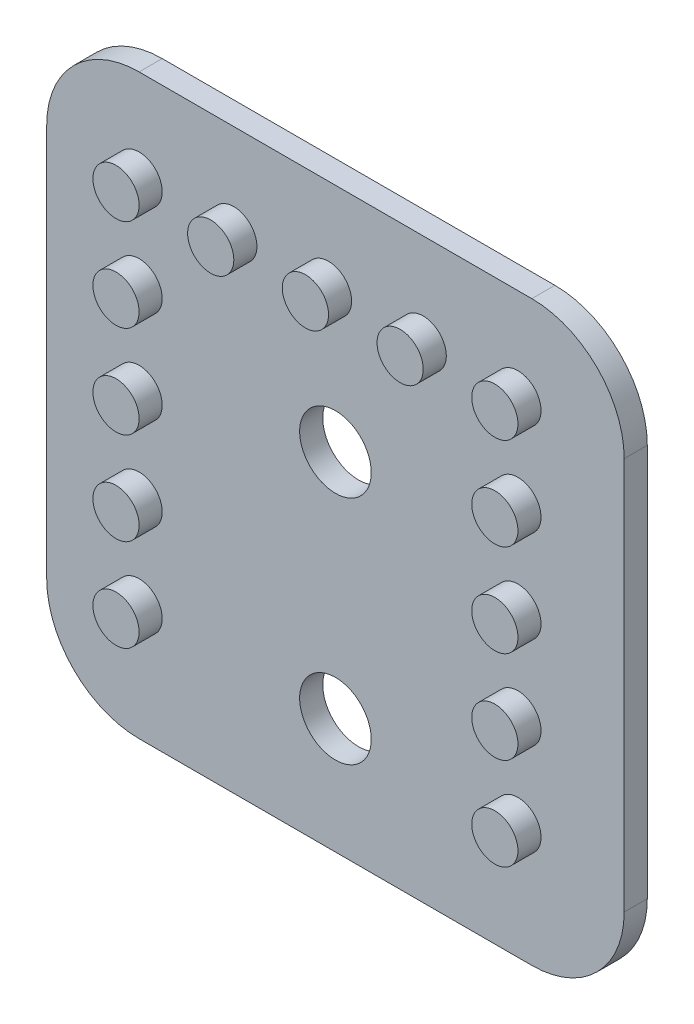
SolidWorks part; units mm, degrees
ref_plane "Front Plane" through (0, 0, 0) normal (0, 0, 1) x (1, 0, 0)
ref_plane "Top Plane" through (0, 0, 0) normal (0, 1, 0) x (1, 0, 0)
ref_plane "Right Plane" through (0, 0, 0) normal (1, 0, 0) x (0, 0, -1)
sketch "Sketch1" plane through (0, 0, 0) normal (0, 0, 1) x (1, 0, 0)
  line L0 (-3, 7) -> (-3, 16) construction
  line L1 (-11, 8) -> (-36, 8)
  line L2 (-11, 8) -> (-11, 33)
  line L3 (-11, 33) -> (-36, 33)
  line L4 (-36, 8) -> (-36, 33)
  line L5 (-191, 0) -> (0, 0) construction
  dimension "D1" = 8
  dimension "D2" = 8
  dimension "D3" = 25
  dimension "D4" = 25
extrude "Boss-Extrude1" add sketch "Sketch1" along normal blind 1
sketch "Sketch2" plane through (0, 0, 1) normal (0, 0, 1) x (1, 0, 0)
  line L0 (-11, 33) -> (-36, 33) construction
  line L1 (-36, 33) -> (-36, 8) construction
  circle A0 centre (-32, 29) radius 1
  circle A1 centre (-27.9, 29) radius 1
  circle A2 centre (-23.8, 29) radius 1
  circle A3 centre (-19.7, 29) radius 1
  circle A4 centre (-15.6, 29) radius 1
  circle A5 centre (-32, 25) radius 1
  circle A6 centre (-15.6, 25) radius 1
  circle A7 centre (-32, 21) radius 1
  circle A8 centre (-15.6, 21) radius 1
  circle A9 centre (-32, 17) radius 1
  circle A10 centre (-15.6, 17) radius 1
  circle A11 centre (-32, 13) radius 1
  circle A12 centre (-15.6, 13) radius 1
  dimension "D1" = 2
  dimension "D2" = 4
  dimension "D3" = 4
  dimension "D4" = 5
  dimension "D5" = 5
extrude "Boss-Extrude2" add sketch "Sketch2" along normal blind 1
fillet "Fillet1" radius 4 4 edges at (-36, 8, 0.5) (-11, 8, 0.5) (-11, 33, 0.5) (-36, 33, 0.5)
sketch "Sketch3" plane through (0, 0, 1) normal (0, 0, 1) x (1, 0, 0)
  line L0 (-15, 33) -> (-32, 33) construction
  circle A0 centre (-23.5, 23) radius 1.55
  circle A1 centre (-23.5, 13) radius 1.55
  dimension "D1" = 3.1
  dimension "D2" = 3.1
  dimension "D3" = 10
  dimension "D4" = 10
extrude "Cut-Extrude1" cut sketch "Sketch3" against normal up to next
